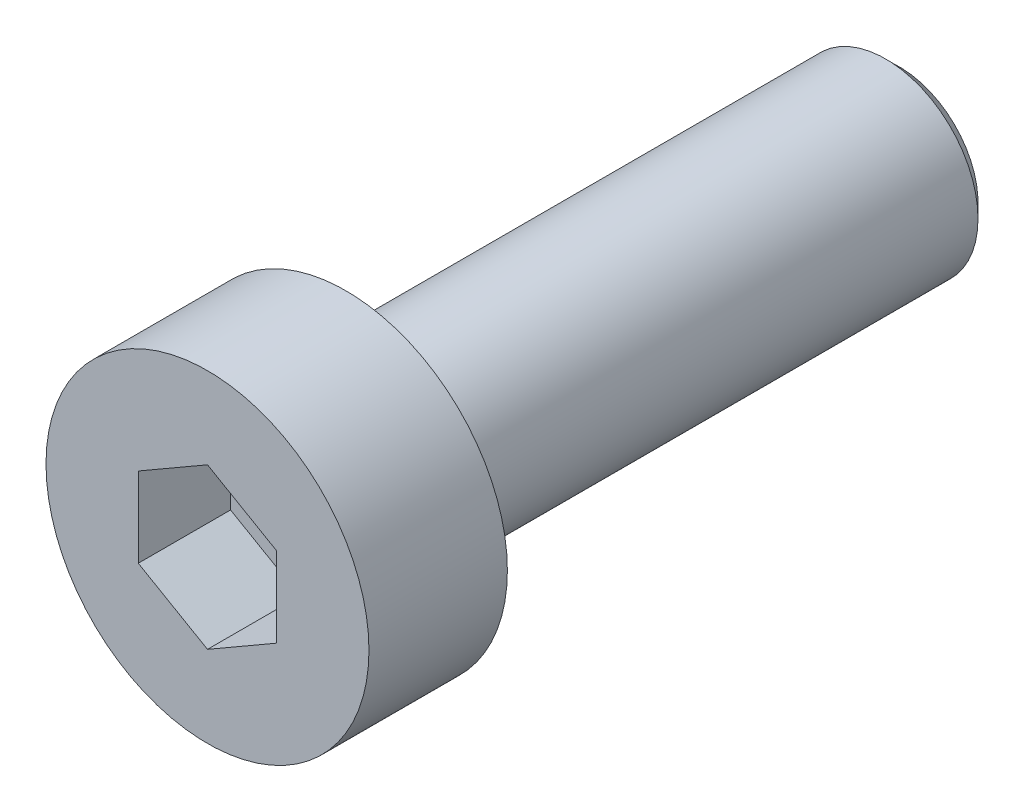
SolidWorks part; units mm, degrees
ref_plane "Front Plane" through (0, 0, 0) normal (0, 0, 1) x (1, 0, 0)
ref_plane "Top Plane" through (0, 0, 0) normal (0, 1, 0) x (1, 0, 0)
ref_plane "Right Plane" through (0, 0, 0) normal (1, 0, 0) x (0, 0, -1)
sketch "Sketch1" plane through (0, 0, 0) normal (0, 0, 1) x (1, 0, 0)
  circle A0 centre (0, 0) radius 3.5
  dimension "D1" = 7
extrude "Boss-Extrude1" add sketch "Sketch1" along normal blind 3
sketch "Sketch2" plane through (0, 0, 0) normal (0, 0, -1) x (-1, 0, 0)
  circle A0 centre (0, 0) radius 2
  dimension "D1" = 4
extrude "Boss-Extrude2" add sketch "Sketch2" along normal blind 12
chamfer "Chamfer1" distance 0.3 angle 45 1 edges at (-2, 0, -12)
sketch "Sketch3" plane through (0, 0, 3) normal (0, 0, 1) x (1, 0, 0)
  line L1 (0, 1.7321) -> (-1.5, 0.866)
  line L2 (-1.5, 0.866) -> (-1.5, -0.866)
  line L3 (-1.5, -0.866) -> (0, -1.7321)
  line L4 (0, -1.7321) -> (1.5, -0.866)
  line L5 (1.5, -0.866) -> (1.5, 0.866)
  line L6 (1.5, 0.866) -> (0, 1.7321)
  circle A0 centre (0, 0) radius 1.5 construction
  dimension "D1" = 3
extrude "Cut-Extrude1" cut sketch "Sketch3" against normal blind 2
